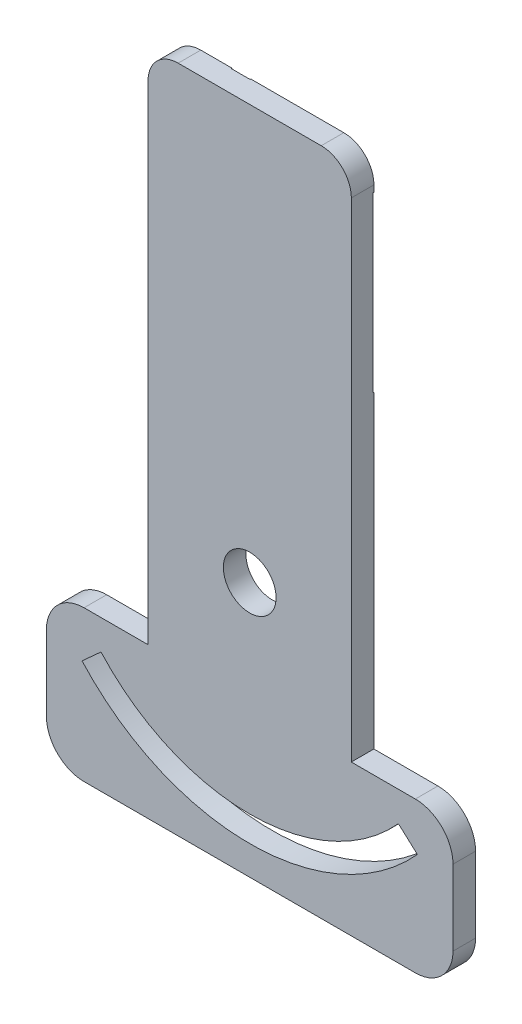
SolidWorks part; units mm, degrees
ref_plane "Alzado" through (0, 0, 0) normal (0, 0, 1) x (1, 0, 0)
ref_plane "Planta" through (0, 0, 0) normal (0, 1, 0) x (1, 0, 0)
ref_plane "Vista lateral" through (0, 0, 0) normal (1, 0, 0) x (0, 0, -1)
sketch "Corte exterior" plane through (0, 0, 0) normal (0, 0, 1) x (1, 0, 0)
  line L0 (19.522, -6.0858) -> (11.022, -6.0858)
  line L1 (46.5148, -6.0858) -> (55.022, -6.0858)
  line L2 (11.022, -26.0858) -> (55.022, -26.0858)
  line L3 (42.522, 62.812) -> (23.522, 62.812)
  line L4 (46.5148, -6.0858) -> (46.522, 58.812)
  line L5 (55.2949, -12.3304) -> (52.7732, -10.0498)
  line L6 (13.2708, -10.0498) -> (10.749, -12.3304)
  line L7 (60.0153, -11.0858) -> (60.0153, -21.0858)
  line L8 (60.022, -11.0858) -> (60.022, -21.0858)
  line L9 (6.022, -11.0858) -> (6.022, -21.0858)
  line L10 (19.522, 58.812) -> (19.522, -6.0858)
  arc A0 (23.522, 62.812) -> (19.522, 58.812) centre (23.522, 58.812) ccw
  arc A1 (46.522, 58.812) -> (42.522, 62.812) centre (42.522, 58.812) ccw
  circle A2 centre (33.022, 7.812) radius 3.5
  arc A3 (6.022, -21.0858) -> (11.022, -26.0858) centre (11.022, -21.0858) ccw
  arc A4 (55.022, -26.0858) -> (60.022, -21.0858) centre (55.022, -21.0858) ccw
  arc A5 (60.022, -11.0858) -> (55.022, -6.0858) centre (55.022, -11.0858) ccw
  arc A6 (11.022, -6.0858) -> (6.022, -11.0858) centre (11.022, -11.0858) ccw
  arc A7 (10.749, -12.3304) -> (55.2949, -12.3304) centre (33.022, 7.812) ccw
  arc A8 (13.2708, -10.0498) -> (52.7732, -10.0498) centre (33.022, 7.812) ccw
sketch "Grabado Superficie" plane through (0, 0, 0) normal (0, 0, 1) x (1, 0, 0)
  line L0 (35.8913, 9.8162) -> (35.017, 22.2029)
  line L1 (31.027, 22.2029) -> (30.1526, 9.8162)
  arc A0 (35.017, 22.2029) -> (31.027, 22.2029) centre (33.022, 22.062) ccw
  arc A1 (35.8913, 9.8162) -> (30.1526, 9.8162) centre (33.022, 7.812) ccw
sketch "grabado linea medio" plane through (0, 0, 0) normal (0, 0, 1) x (1, 0, 0)
  line L0 (23.602, 43.022) -> (19.522, 43.022)
  line L1 (23.602, 34.942) -> (23.602, 43.022)
  line L2 (27.662, 34.942) -> (23.602, 34.942)
  line L3 (27.662, 30.302) -> (27.662, 34.942)
  line L4 (30.182, 30.302) -> (27.662, 30.302)
  line L5 (30.182, 34.942) -> (30.182, 30.302)
  line L6 (46.522, 34.942) -> (30.182, 34.942)
  line L7 (30.182, 58.1708) -> (46.522, 57.9708)
  line L8 (30.182, 62.812) -> (30.182, 58.1708)
  line L9 (27.662, 58.172) -> (27.662, 62.812)
  line L10 (19.522, 58.172) -> (27.662, 58.172)
  line L11 (46.522, 57.9708) -> (46.522, 34.942)
  line L12 (19.522, 43.022) -> (19.522, 58.172)
  line L13 (27.662, 62.812) -> (30.182, 62.812)
extrude "Saliente-Extruir1" add sketch "Corte exterior" along normal blind 3
extrude "Cortar-Extruir1" cut sketch "Grabado Superficie" along normal blind 1
extrude "Cortar-Extruir2" cut sketch "grabado linea medio" along normal blind 0.1
